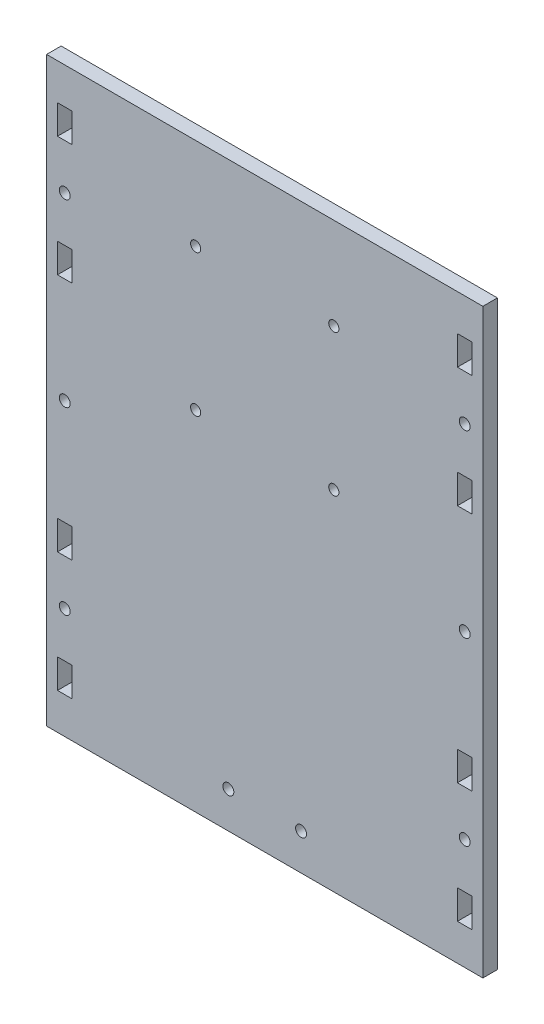
SolidWorks part; units mm, degrees
ref_plane "Front Plane" through (0, 0, 0) normal (0, 0, 1) x (1, 0, 0)
ref_plane "Top Plane" through (0, 0, 0) normal (0, 1, 0) x (1, 0, 0)
ref_plane "Right Plane" through (0, 0, 0) normal (1, 0, 0) x (0, 0, -1)
sketch "Sketch1" plane through (0, 0, 0) normal (0, 0, 1) x (1, 0, 0)
  line L1 (-60, 80) -> (60, 80)
  line L2 (-60, 80) -> (-60, -80)
  line L3 (-60, -80) -> (60, -80)
  line L4 (60, 80) -> (60, -80)
  line L11 (57, -70) -> (53, -70)
  line L12 (57, 70) -> (53, 70)
  line L13 (53, 70) -> (53, 62)
  line L14 (57, 70) -> (57, 62)
  line L15 (-10, 80) -> (10, 80)
  line L16 (53, 62) -> (57, 62)
  line L23 (53, 29) -> (57, 29)
  line L24 (57, 37) -> (53, 37)
  line L26 (53, 37) -> (53, 29)
  line L27 (57, 37) -> (57, 29)
  line L28 (53, -62) -> (57, -62)
  line L30 (57, -37) -> (53, -37)
  line L31 (53, -37) -> (53, -29)
  line L32 (53, -29) -> (57, -29)
  line L33 (53, -62) -> (53, -70)
  line L34 (57, -62) -> (57, -70)
  line L35 (53, -29) -> (53, -37)
  line L36 (57, -29) -> (57, -37)
  line L37 (-57, -37) -> (-53, -37)
  line L38 (-57, -29) -> (-57, -37)
  line L39 (-53, -29) -> (-57, -29)
  line L40 (-53, -37) -> (-53, -29)
  line L41 (-57, 37) -> (-57, 29)
  line L42 (-53, 29) -> (-57, 29)
  line L43 (-53, 37) -> (-53, 29)
  line L44 (-57, 37) -> (-53, 37)
  line L45 (-57, 70) -> (-57, 62)
  line L46 (-53, 62) -> (-57, 62)
  line L47 (-53, 70) -> (-53, 62)
  line L48 (-57, 70) -> (-53, 70)
  line L49 (-53, -62) -> (-53, -70)
  line L50 (-57, -70) -> (-53, -70)
  line L51 (-57, -62) -> (-57, -70)
  line L52 (-53, -62) -> (-57, -62)
  line L53 (-55, 62) -> (-55, 37) construction
  line L54 (-55, 29) -> (-55, -29) construction
  line L55 (-55, -62) -> (-55, -37) construction
  circle A1 centre (-10, -70) radius 1.5
  circle A2 centre (10, -70) radius 1.5
  circle A4 centre (-19, 54.8) radius 1.4
  circle A5 centre (19, 54.8) radius 1.4
  circle A6 centre (-19, 15.8) radius 1.4
  circle A7 centre (19, 15.8) radius 1.4
  circle A8 centre (-55, -49.5) radius 1.5
  circle A9 centre (-55, 0) radius 1.5
  circle A10 centre (-55, 49.5) radius 1.5
  circle A11 centre (55, -49.5) radius 1.5
  circle A12 centre (55, 0) radius 1.5
  circle A13 centre (55, 49.5) radius 1.5
  point P0 (0, 0)
  point P16 (0, 35.8)
  point P27 (0, 80)
  point P38 (55, 70)
  dimension "D8" = 3
  dimension "D12" = 2.8
  dimension "D15" = 2.8
  dimension "D5" = 3
  dimension "D6" = 3
  dimension "D25" = 3
  dimension "D1" = 120
  dimension "D2" = 160
  dimension "D3" = 4
  dimension "D4" = 3
  dimension "D10" = 10
  dimension "D13" = 20
  dimension "D19" = 8
  dimension "D20" = 25
  dimension "D21" = 8
  dimension "D22" = 8
  dimension "D23" = 25
  dimension "D24" = 8
extrude "Boss-Extrude2" add sketch "Sketch1" along normal blind 4 contours L4 L1 L2 L3 A12 A7 A6 A2 A1 L52 L49 L50 L51 L40 L37 L38 L39 L16 L13 L12 L14 L24 L27 L23 L26 L28 L34 L11 L33 L32 L36 L30 L31 L41 L44 L43 L42
